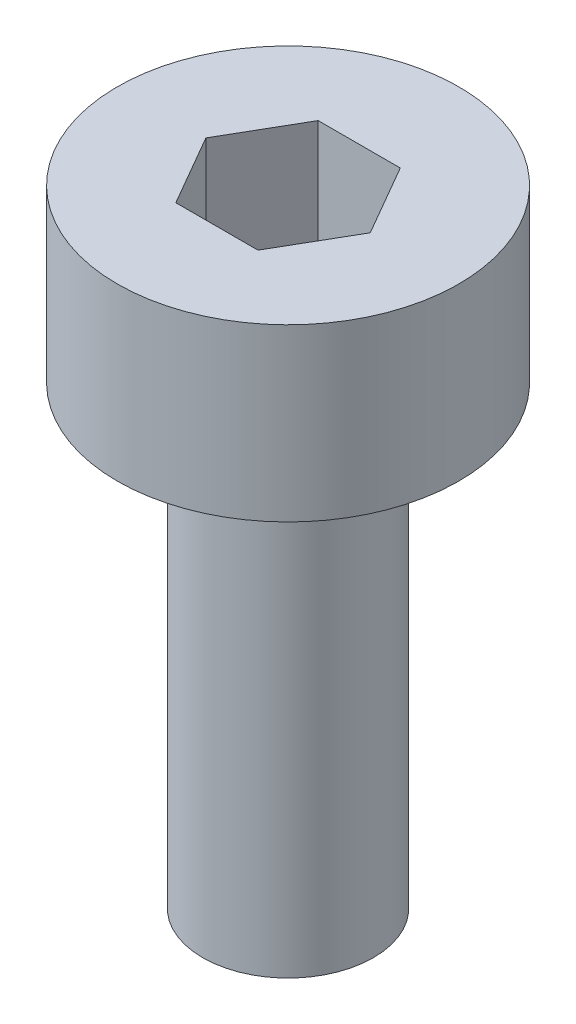
SolidWorks part; units mm, degrees
ref_plane "Front Plane" through (0, 0, 0) normal (0, 0, 1) x (1, 0, 0)
ref_plane "Top Plane" through (0, 0, 0) normal (0, 1, 0) x (1, 0, 0)
ref_plane "Right Plane" through (0, 0, 0) normal (1, 0, 0) x (0, 0, -1)
sketch "Sketch1" plane through (0, 0, 0) normal (0, 1, 0) x (1, 0, 0)
  circle A0 centre (0, 0) radius 1.5
  dimension "D1" = 3
extrude "Boss-Extrude1" add sketch "Sketch1" along normal blind 8
sketch "Sketch2" plane through (0, 8, 0) normal (0, 1, 0) x (1, 0, 0)
  circle A0 centre (0, 0) radius 3
  dimension "D1" = 6
extrude "Boss-Extrude2" add sketch "Sketch2" along normal blind 3
sketch "Sketch3" plane through (0, 11, 0) normal (0, 1, 0) x (1, 0, 0)
  line L1 (1.4434, 0) -> (0.7217, 1.25)
  line L2 (0.7217, 1.25) -> (-0.7217, 1.25)
  line L3 (-0.7217, 1.25) -> (-1.4434, 0)
  line L4 (-1.4434, 0) -> (-0.7217, -1.25)
  line L5 (-0.7217, -1.25) -> (0.7217, -1.25)
  line L6 (0.7217, -1.25) -> (1.4434, 0)
  circle A0 centre (0, 0) radius 1.25 construction
  dimension "D1" = 2.5
extrude "Cut-Extrude1" cut sketch "Sketch3" against normal blind 2
